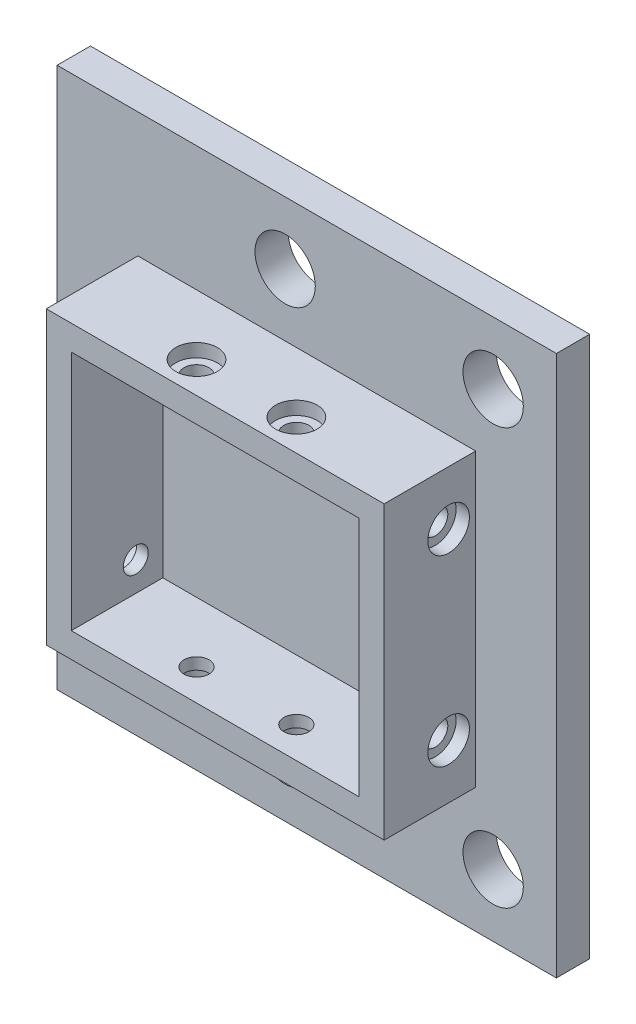
SolidWorks part; units mm, degrees
ref_plane "정면" through (0, 0, 0) normal (0, 0, 1) x (1, 0, 0)
ref_plane "윗면" through (0, 0, 0) normal (0, 1, 0) x (1, 0, 0)
ref_plane "우측면" through (0, 0, 0) normal (1, 0, 0) x (0, 0, -1)
sketch "스케치1" plane through (0, 0, 0) normal (0, 0, 1) x (1, 0, 0)
  line L0 (0, 32.5) -> (0, -32.5) construction
  line L1 (30, -32.5) -> (-30, -32.5)
  line L2 (30, -32.5) -> (30, 32.5)
  line L3 (30, 32.5) -> (-30, 32.5)
  line L4 (-30, -32.5) -> (-30, 32.5)
  line L5 (30, -32.5) -> (-30, 32.5) construction
  line L6 (30, 32.5) -> (-30, -32.5) construction
  line L7 (-2.6, 32.5) -> (-2.6, -32.5) construction
  line L8 (22.4, 32.5) -> (22.4, -32.5) construction
  line L10 (17, -14.25) -> (-17, -14.25) construction
  line L11 (17, -14.25) -> (17, 14.25) construction
  line L12 (17, 14.25) -> (-17, 14.25) construction
  line L13 (-17, -14.25) -> (-17, 14.25) construction
  line L14 (17, -14.25) -> (-17, 14.25) construction
  line L15 (17, 14.25) -> (-17, -14.25) construction
  circle A0 centre (-2.6, 25) radius 3.625
  circle A1 centre (-2.6, -25) radius 3.625
  circle A2 centre (22.4, 25) radius 3.625
  circle A3 centre (22.4, -25) radius 3.625
  point P0 (0, 0)
  point P12 (0, 0)
  point P25 (0, 0)
  point P26 (0, 0)
  point P27 (-2.6, 0)
  dimension "D7" = 7.25
  dimension "D1" = 2.6
  dimension "D2" = 25
  dimension "D3" = 28.5
  dimension "D4" = 34
  dimension "D5" = 65
  dimension "D6" = 60
  dimension "D8" = 25
  dimension "D9" = 25
extrude "보스-돌출1" add sketch "스케치1" along normal blind 4
sketch "스케치2" plane through (0, 0, 4) normal (0, 0, 1) x (1, 0, 0)
  line L1 (17.3, -14.5) -> (-17.3, -14.5)
  line L2 (17.3, -14.5) -> (17.3, 14.5)
  line L3 (17.3, 14.5) -> (-17.3, 14.5)
  line L4 (-17.3, -14.5) -> (-17.3, 14.5)
  line L5 (17.3, -14.5) -> (-17.3, 14.5) construction
  line L6 (17.3, 14.5) -> (-17.3, -14.5) construction
  line L7 (20.3, -17.5) -> (-20.3, -17.5)
  line L8 (20.3, -17.5) -> (20.3, 17.5)
  line L9 (20.3, 17.5) -> (-20.3, 17.5)
  line L10 (-20.3, -17.5) -> (-20.3, 17.5)
  line L11 (20.3, -17.5) -> (-20.3, 17.5) construction
  line L12 (20.3, 17.5) -> (-20.3, -17.5) construction
  point P0 (0, 0)
  point P6 (0, 0)
  dimension "D1" = 34.6
  dimension "D2" = 29
  dimension "D3" = 35
  dimension "D4" = 40.6
extrude "보스-돌출2" add sketch "스케치2" along normal blind 11
sketch "스케치3" plane through (0, -17.5, 0) normal (0, -1, 0) x (1, 0, 0)
  line L0 (0, 0) -> (0, 15) construction
  line L1 (-30, 0) -> (30, 0) construction
  line L2 (-20.3, 15) -> (20.3, 15) construction
  line L3 (-30, 4) -> (30, 4) construction
  circle A0 centre (-6, 11.25) radius 1.5
  circle A1 centre (6, 11.25) radius 1.5
  dimension "D1" = 3
  dimension "D2" = 7.25
  dimension "D3" = 12
extrude "컷-돌출1" cut sketch "스케치3" against normal through all
sketch "스케치4" plane through (0, -17.5, 0) normal (0, -1, 0) x (1, 0, 0)
  line L0 (0, 0) -> (0, 15) construction
  line L1 (-20.3, 15) -> (20.3, 15) construction
  circle A0 centre (-6, 11.25) radius 2.5
  circle A1 centre (6, 11.25) radius 2.5
  dimension "D1" = 5
extrude "컷-돌출2" cut sketch "스케치4" against normal blind 1.6
mirror "대칭 복사1" about plane through (0, 0, 0) normal (0, 1, 0) of "컷-돌출2"
sketch "스케치5" plane through (-20.3, 0, 0) normal (-1, 0, 0) x (0, 0, 1)
  line L0 (0, 0) -> (15, 0) construction
  line L1 (0, 32.5) -> (0, -32.5) construction
  line L2 (15, 17.5) -> (15, -17.5) construction
  line L3 (4, 32.5) -> (4, -32.5) construction
  circle A0 centre (7.25, -11) radius 1.5
  circle A1 centre (7.25, 11) radius 1.5
  dimension "D1" = 3
  dimension "D2" = 11
  dimension "D3" = 3.25
extrude "컷-돌출3" cut sketch "스케치5" against normal through all
sketch "스케치6" plane through (-20.3, 0, 0) normal (-1, 0, 0) x (0, 0, 1)
  line L0 (0, 0) -> (15, 0) construction
  line L1 (15, 17.5) -> (15, -17.5) construction
  circle A0 centre (7.25, 11) radius 2.5
  circle A1 centre (7.25, -11) radius 2.5
  dimension "D1" = 5
extrude "컷-돌출4" cut sketch "스케치6" against normal blind 1.6
mirror "대칭 복사2" about plane through (0, 0, 0) normal (1, 0, 0) of "컷-돌출4"
